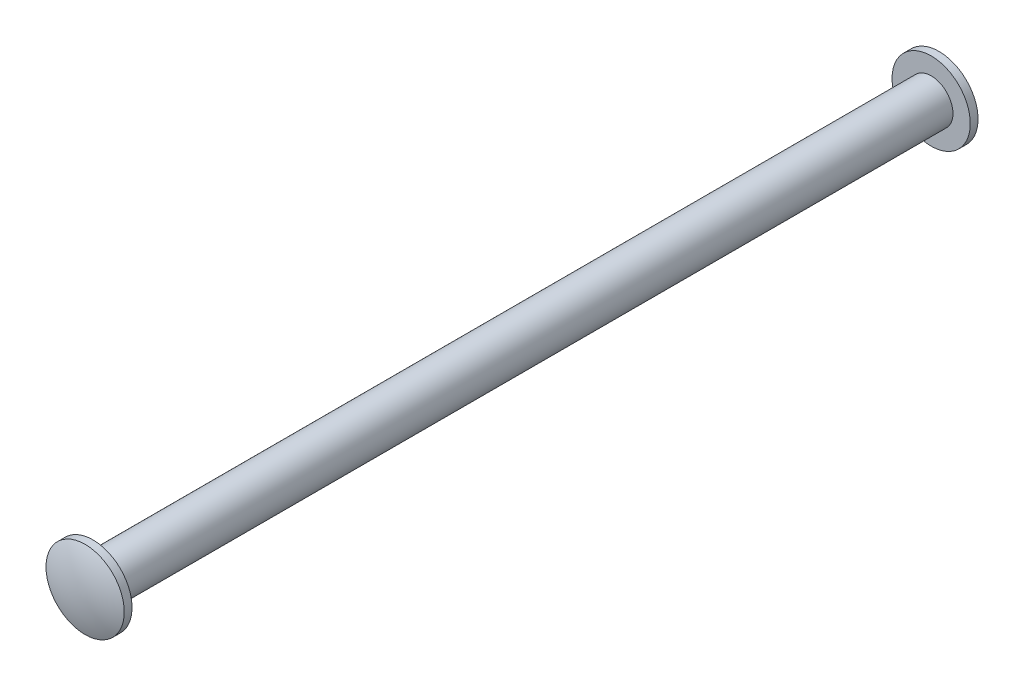
SolidWorks part; units mm, degrees
ref_plane "Front Plane" through (0, 0, 0) normal (0, 0, 1) x (1, 0, 0)
ref_plane "Top Plane" through (0, 0, 0) normal (0, 1, 0) x (1, 0, 0)
ref_plane "Right Plane" through (0, 0, 0) normal (1, 0, 0) x (0, 0, -1)
ref_plane "Plane1" through (0, 0, 0) normal (0, -1, 0) x (1, 0, 0)
sketch "Sketch1" plane through (0, 0, 0) normal (0, -1, 0) x (1, 0, 0)
  line L0 (0, 39.5173) -> (0, -39.5173)
  line L1 (3.556, -38.8087) -> (3.556, -38.1)
  line L2 (3.556, -38.1) -> (1.9844, -38.1)
  line L3 (1.9844, -38.1) -> (1.9844, 38.1)
  line L4 (1.9844, 38.1) -> (3.556, 38.1)
  line L5 (3.556, 38.1) -> (3.556, 38.8087)
  line L6 (0, 39.5173) -> (0, -39.5173) construction
  arc A0 (3.556, 38.8087) -> (0, 39.5173) centre (0, 30.2411) ccw
  arc A1 (0, -39.5173) -> (3.556, -38.8087) centre (0, -30.2411) ccw
revolve "Revolve1" add sketch "Sketch1" angle 360 about L6
